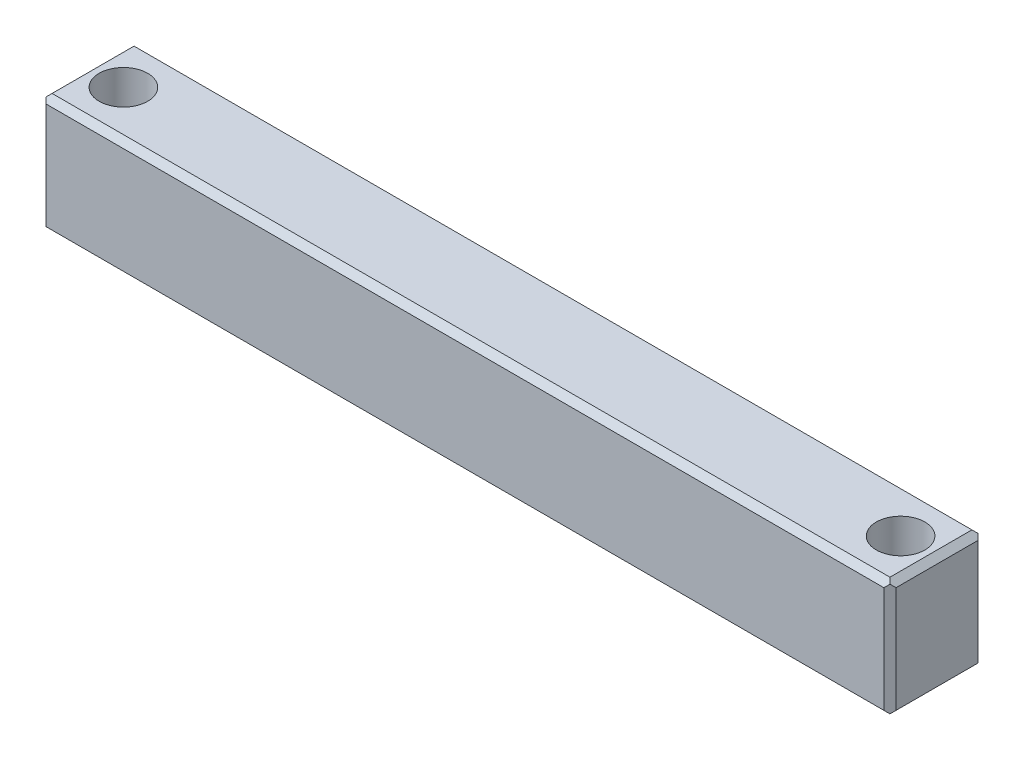
SolidWorks part; units mm, degrees
ref_plane "Front Plane" through (0, 0, 0) normal (0, 0, 1) x (1, 0, 0)
ref_plane "Top Plane" through (0, 0, 0) normal (0, 1, 0) x (1, 0, 0)
ref_plane "Right Plane" through (0, 0, 0) normal (1, 0, 0) x (0, 0, -1)
sketch "Sketch1" plane through (0, 0, 0) normal (1, 0, 0) x (0, 0, -1)
  line L1 (0, 0) -> (7.75, 0)
  line L2 (0, 0) -> (0, 9.75)
  line L3 (0, 9.75) -> (7.75, 9.75)
  line L4 (7.75, 0) -> (7.75, 9.75)
  dimension "D1" = 7.75
  dimension "D2" = 9.75
extrude "Boss-Extrude1" add sketch "Sketch1" along normal blind 70
sketch "Sketch4" plane through (0, 9.75, 0) normal (0, 1, 0) x (1, 0, 0)
  line L0 (0, 3.875) -> (3, 3.875) construction
  line L1 (0, 7.75) -> (0, 0) construction
  line L2 (70, 3.875) -> (67, 3.875) construction
  line L3 (70, 7.75) -> (70, 0) construction
  circle A2 centre (3, 3.875) radius 2
  circle A3 centre (67, 3.875) radius 2
  dimension "D2" = 3
  dimension "D1" = 3
extrude "Cut-Extrude3" cut sketch "Sketch4" against normal up to surface (9.75 mm away) up to face at (35, 0, -3.875)
chamfer "Chamfer1" distance 0.5 angle 45 8 edges at (0, 0, -3.875) (0, 4.875, -7.75) (0, 9.75, -3.875) (0, 4.875, 0) (70, 9.75, -3.875) (70, 4.875, -7.75) (70, 0, -3.875) (70, 4.875, 0)
chamfer "Chamfer2" distance 0.5 angle 45 4 edges at (35, 9.75, 0) (35, 0, 0) (35, 9.75, -7.75) (35, 0, -7.75)
